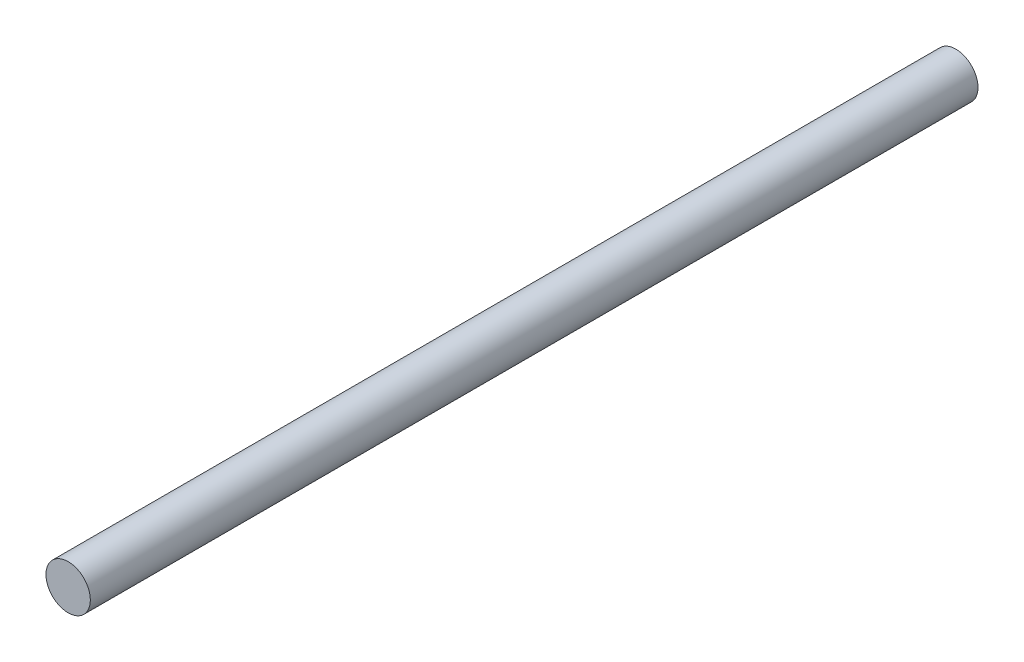
SolidWorks part; units mm, degrees
ref_plane "Front Plane" through (0, 0, 0) normal (0, 0, 1) x (1, 0, 0)
ref_plane "Top Plane" through (0, 0, 0) normal (0, 1, 0) x (1, 0, 0)
ref_plane "Right Plane" through (0, 0, 0) normal (1, 0, 0) x (0, 0, -1)
sketch "Sketch1" plane through (0, 0, 0) normal (0, 0, 1) x (1, 0, 0)
  circle A0 centre (0, 0) radius 4.5
  dimension "D1" = 9
extrude "Boss-Extrude1" add sketch "Sketch1" along normal blind 180
